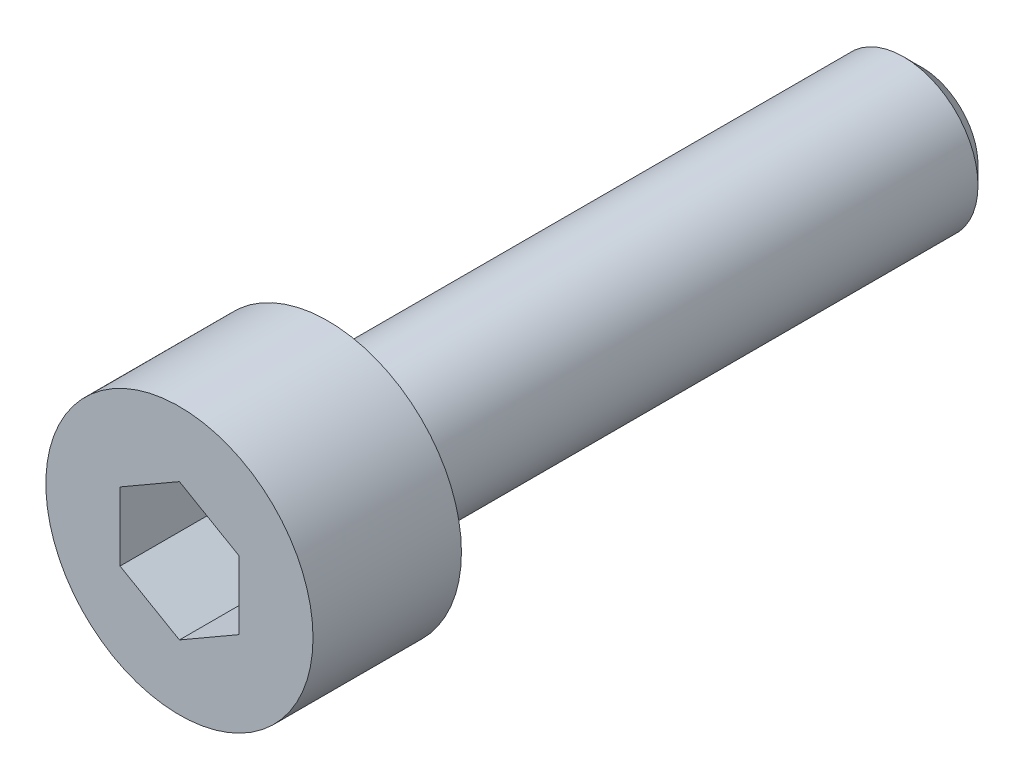
SolidWorks part; units mm, degrees
ref_plane "Front Plane" through (0, 0, 0) normal (0, 0, 1) x (1, 0, 0)
ref_plane "Top Plane" through (0, 0, 0) normal (0, 1, 0) x (1, 0, 0)
ref_plane "Right Plane" through (0, 0, 0) normal (1, 0, 0) x (0, 0, -1)
sketch "Sketch1" plane through (0, 0, 0) normal (0, 0, 1) x (1, 0, 0)
  circle A0 centre (0, 0) radius 2.25
  dimension "D1" = 4.5
extrude "Boss-Extrude1" add sketch "Sketch1" along normal blind 2.5
sketch "Sketch2" plane through (0, 0, 0) normal (0, 0, -1) x (-1, 0, 0)
  circle A0 centre (0, 0) radius 1.25
  dimension "D1" = 2.5
extrude "Boss-Extrude2" add sketch "Sketch2" along normal blind 10
chamfer "Chamfer1" distance 0.3 angle 45 1 edges at (-1.25, 0, -10)
sketch "Sketch3" plane through (0, 0, 2.5) normal (0, 0, 1) x (1, 0, 0)
  line L1 (0, 1.1547) -> (-1, 0.5774)
  line L2 (-1, 0.5774) -> (-1, -0.5774)
  line L3 (-1, -0.5774) -> (0, -1.1547)
  line L4 (0, -1.1547) -> (1, -0.5774)
  line L5 (1, -0.5774) -> (1, 0.5774)
  line L6 (1, 0.5774) -> (0, 1.1547)
  circle A0 centre (0, 0) radius 1 construction
  dimension "D1" = 2
extrude "Cut-Extrude1" cut sketch "Sketch3" against normal blind 2
